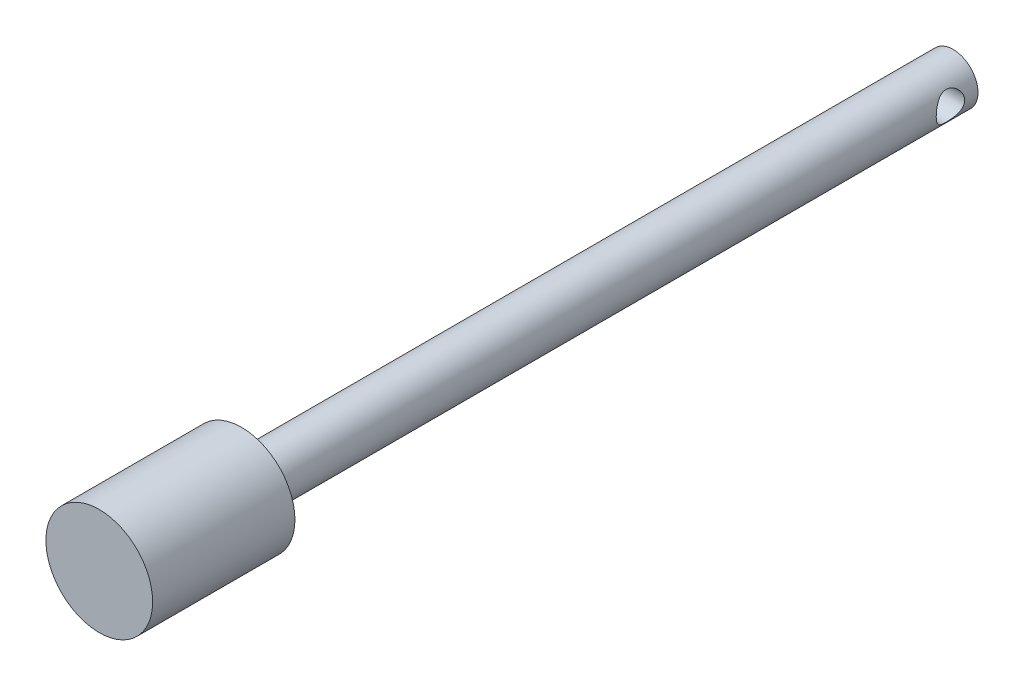
SolidWorks part; units mm, degrees
ref_plane "Front Plane" through (0, 0, 0) normal (0, 0, 1) x (1, 0, 0)
ref_plane "Top Plane" through (0, 0, 0) normal (0, 1, 0) x (1, 0, 0)
ref_plane "Right Plane" through (0, 0, 0) normal (1, 0, 0) x (0, 0, -1)
sketch "Sketch1" plane through (0, 0, 0) normal (0, 0, 1) x (1, 0, 0)
  circle A0 centre (0, 0) radius 3.5
  dimension "D1" = 7
extrude "Boss-Extrude1" add sketch "Sketch1" along normal blind 100
sketch "Sketch2" plane through (0, 0, 100) normal (0, 0, 1) x (1, 0, 0)
  circle A0 centre (0, 0) radius 7.5
  dimension "D1" = 15
extrude "Boss-Extrude2" add sketch "Sketch2" along normal blind 20
sketch "Sketch3" plane through (0, 0, 0) normal (1, 0, 0) x (0, 0, -1)
  line L0 (-126.1005, 0) -> (10.6719, 0) construction
  line L1 (0, 16.2471) -> (-7.7374, 16.2471) construction
  line L2 (-3.8687, 16.2471) -> (-3.8687, -11.305) construction
  circle A0 centre (-3.8687, 0) radius 2
  point P7 (-3.8687, 0)
  dimension "D1" = 4
extrude "Cut-Extrude1" cut sketch "Sketch3" against normal through all both and the other way through all
